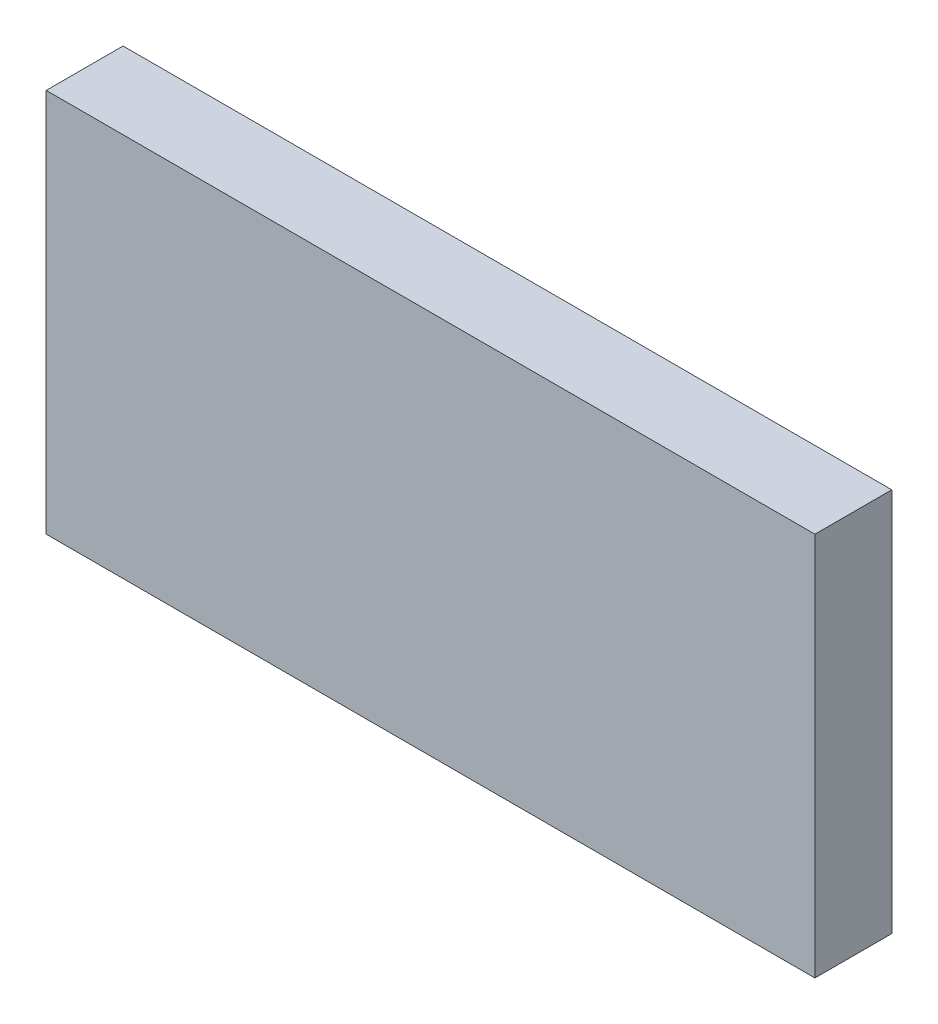
SolidWorks part; units mm, degrees
ref_plane "前视基准面" through (0, 0, 0) normal (0, 0, 1) x (1, 0, 0)
ref_plane "上视基准面" through (0, 0, 0) normal (0, 1, 0) x (1, 0, 0)
ref_plane "右视基准面" through (0, 0, 0) normal (1, 0, 0) x (0, 0, -1)
sketch "草图1" plane through (0, 0, 0) normal (0, 0, 1) x (1, 0, 0)
  line L0 (-39.216, 24.0018) -> (-39.216, 14.0018)
  line L1 (-39.216, 14.0018) -> (-19.216, 14.0018)
  line L2 (-19.216, 14.0018) -> (-19.216, 24.0018)
  line L3 (-19.216, 24.0018) -> (-39.216, 24.0018)
  dimension "D1" = 10
  dimension "D2" = 20
extrude "凸台-拉伸1" add sketch "草图1" along normal blind 2
